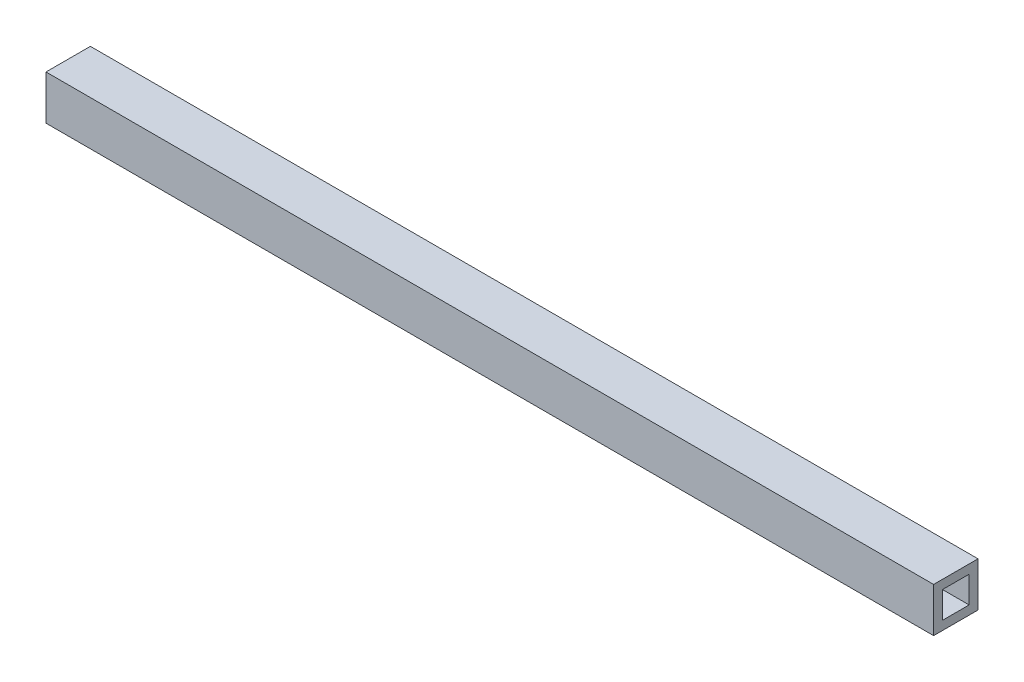
SolidWorks part; units mm, degrees
ref_plane "Front Plane" through (0, 0, 0) normal (0, 0, 1) x (1, 0, 0)
ref_plane "Top Plane" through (0, 0, 0) normal (0, 1, 0) x (1, 0, 0)
ref_plane "Right Plane" through (0, 0, 0) normal (1, 0, 0) x (0, 0, -1)
sketch "Sketch1" plane through (0, 0, 0) normal (1, 0, 0) x (0, 0, -1)
  line L1 (-12.5, -12.5) -> (12.5, -12.5)
  line L2 (-12.5, -12.5) -> (-12.5, 12.5)
  line L3 (-12.5, 12.5) -> (12.5, 12.5)
  line L4 (12.5, -12.5) -> (12.5, 12.5)
  line L5 (-12.5, -12.5) -> (12.5, 12.5) construction
  line L6 (-12.5, 12.5) -> (12.5, -12.5) construction
  point P0 (0, 0)
  dimension "D1" = 25
  dimension "D2" = 25
extrude "Boss-Extrude1" add sketch "Sketch1" along normal blind 500
sketch "Sketch2" plane through (500, 0, 0) normal (1, 0, 0) x (0, 0, -1)
  line L1 (-7.5, -7.5) -> (7.5, -7.5)
  line L2 (-7.5, -7.5) -> (-7.5, 7.5)
  line L3 (-7.5, 7.5) -> (7.5, 7.5)
  line L4 (7.5, -7.5) -> (7.5, 7.5)
  line L5 (-7.5, -7.5) -> (7.5, 7.5) construction
  line L6 (-7.5, 7.5) -> (7.5, -7.5) construction
  point P0 (0, 0)
  dimension "D1" = 15
  dimension "D2" = 15
extrude "Cut-Extrude1" cut sketch "Sketch2" against normal through all
